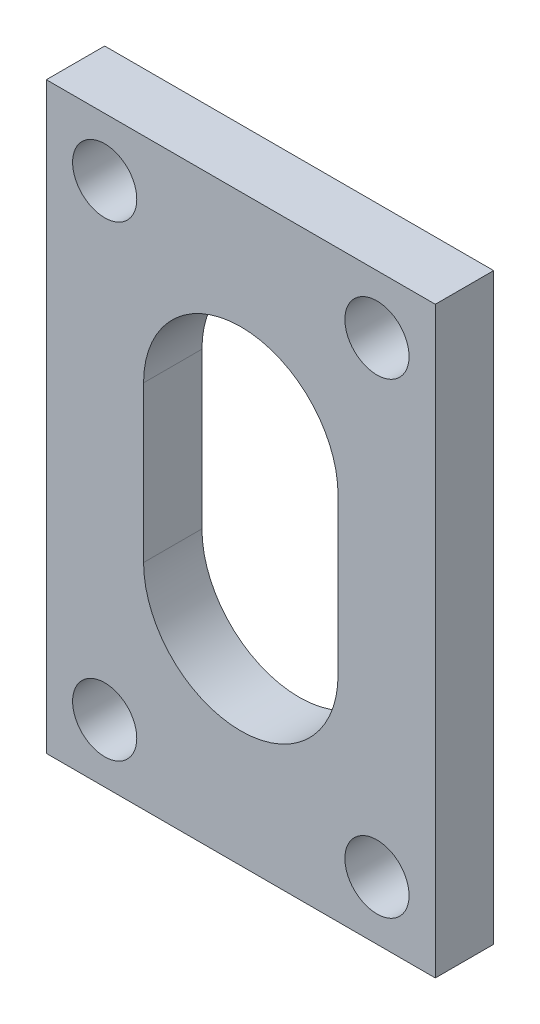
SolidWorks part; units mm, degrees
material "Acrílico (Impacto medio-alto)"
ref_plane "Alzado" through (0, 0, 0) normal (0, 0, 1) x (1, 0, 0)
ref_plane "Planta" through (0, 0, 0) normal (0, 1, 0) x (1, 0, 0)
ref_plane "Vista lateral" through (0, 0, 0) normal (1, 0, 0) x (0, 0, -1)
sketch "Croquis1" plane through (0, 0, 0) normal (0, 0, 1) x (1, 0, 0)
  line L1 (10, -15) -> (-10, -15)
  line L2 (10, -15) -> (10, 15)
  line L3 (10, 15) -> (-10, 15)
  line L4 (-10, -15) -> (-10, 15)
  line L5 (10, -15) -> (-10, 15) construction
  line L6 (10, 15) -> (-10, -15) construction
  circle A0 centre (-7, 12) radius 1.65
  circle A1 centre (7, 12) radius 1.65
  circle A2 centre (7, -12) radius 1.65
  circle A3 centre (-7, -12) radius 1.65
  point P0 (0, 0)
  dimension "D1" = 3.3
  dimension "D4" = 3
  dimension "D5" = 3
  dimension "D6" = 3
  dimension "D7" = 3
  dimension "D8" = 3
  dimension "D2" = 30
  dimension "D3" = 20
extrude "Saliente-Extruir1" add sketch "Croquis1" along normal blind 3
sketch "Croquis2" plane through (0, 0, 3) normal (0, 0, 1) x (1, 0, 0)
  line L0 (0, -4) -> (0, 4) construction
  line L1 (-5, -4) -> (-5, 4)
  line L2 (5, -4) -> (5, 4)
  arc A0 (-5, -4) -> (5, -4) centre (0, -4) ccw
  arc A1 (5, 4) -> (-5, 4) centre (0, 4) ccw
  point P3 (0, 0)
  dimension "D2" = 8
  dimension "D1" = 5
extrude "Cortar-Extruir1" cut sketch "Croquis2" against normal up to next
